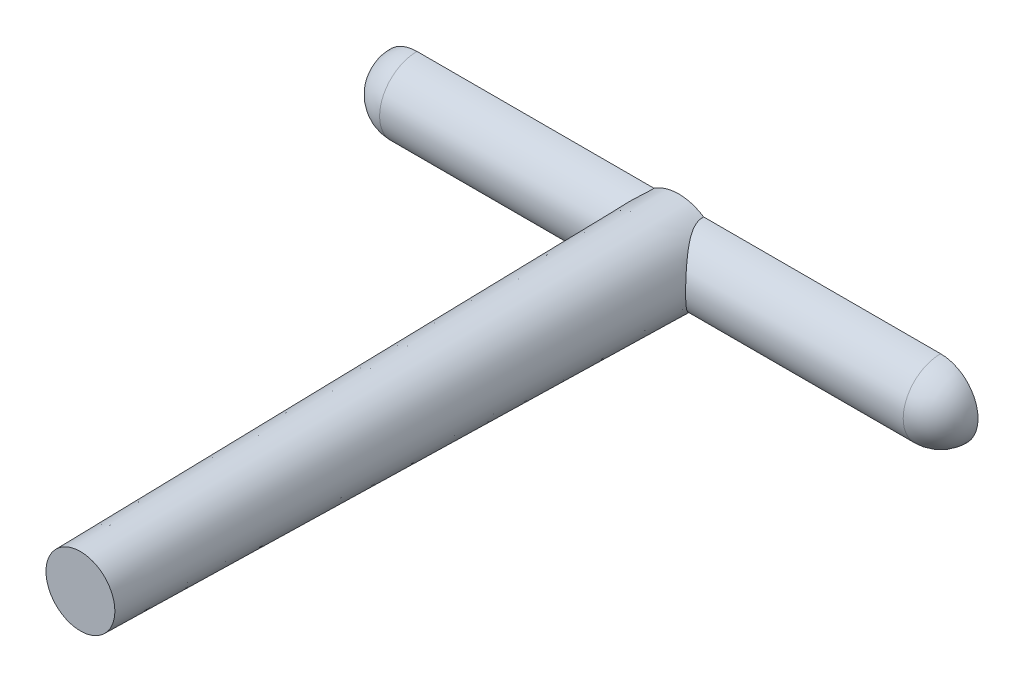
SolidWorks part; units mm, degrees
material "PS Среднего/Высокого потока"
ref_plane "Front Plane" through (0, 0, 0) normal (0, 0, 1) x (1, 0, 0)
ref_plane "Top Plane" through (0, 0, 0) normal (0, 1, 0) x (1, 0, 0)
ref_plane "Right Plane" through (0, 0, 0) normal (1, 0, 0) x (0, 0, -1)
sketch "Sketch1" plane through (0, 0, 0) normal (0, 0, 1) x (1, 0, 0)
  line L0 (-20, 0) -> (20, 0)
  line L1 (-17.5, 2.5) -> (17.5, 2.5)
  arc A0 (17.5, 2.5) -> (20, 0) centre (17.5, 0) cw
  arc A1 (-17.5, 2.5) -> (-20, 0) centre (-17.5, 0) ccw
  dimension "D1" = 2.5
  dimension "D2" = 40
revolve "Revolve1" add sketch "Sketch1" angle 180 about L0
sketch "Sketch2" plane through (0, 0, 0) normal (0, 0, -1) x (-1, 0, 0)
  circle A0 centre (0, 0) radius 3
  dimension "D1" = 6
extrude "Extrude1" add sketch "Sketch2" against normal blind 40 draft 1
